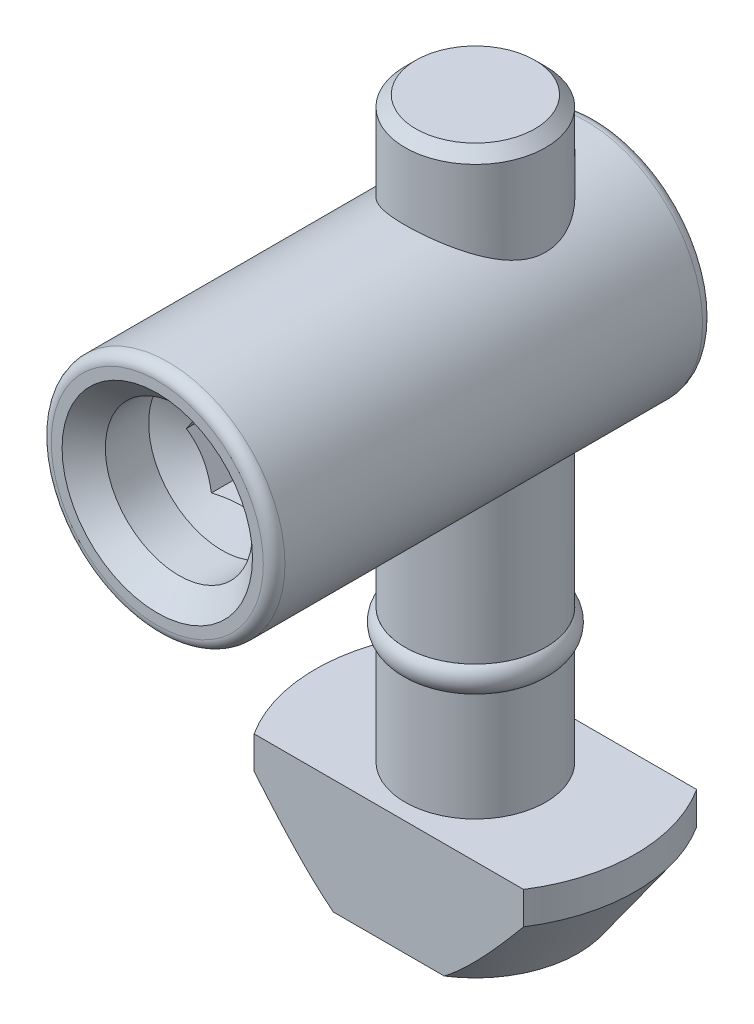
SolidWorks part; units mm, degrees
ref_plane "Спереди" through (0, 0, 0) normal (0, 0, 1) x (1, 0, 0)
ref_plane "Сверху" through (0, 0, 0) normal (0, 1, 0) x (1, 0, 0)
ref_plane "Справа" through (0, 0, 0) normal (1, 0, 0) x (0, 0, -1)
sketch "Эскиз3" plane through (0, 0, 0) normal (0, 0, 1) x (1, 0, 0)
  line L0 (0, 0) -> (-3.25, 0)
  line L1 (-3.25, 0) -> (-3.25, -20.5)
  line L2 (-3.25, -20.5) -> (-2.75, -20.5)
  line L3 (-2.75, -20.5) -> (-2.75, -21.7)
  line L4 (-2.75, -21.7) -> (-3.25, -21.7)
  line L5 (-3.25, -21.7) -> (-3.25, -26.7)
  line L7 (0, -32) -> (0, 0)
  line L8 (0, 0) -> (0, 5.384) construction
  line L9 (-3.25, -26.7) -> (-7.4, -26.7)
  line L10 (-7.4, -26.7) -> (-7.4, -28.2)
  line L11 (-7.4, -28.2) -> (-4.75, -32)
  line L12 (-4.75, -32) -> (0, -32)
  dimension "D1" = 6.5
  dimension "D2" = 1.2
  dimension "D3" = 32
  dimension "D4" = 0.5
  dimension "D5" = 5
  dimension "D6" = 5.3
  dimension "D7" = 1.5
  dimension "D8" = 1.5
  dimension "D9" = 14.8
revolve "Повернуть1" add sketch "Эскиз3" angle 360 about L8
sketch "Эскиз6" plane through (0, -32, 0) normal (0, -1, 0) x (1, 0, 0)
  line L1 (-7.4, -4) -> (7.4, -4)
  line L2 (-7.4, -4) -> (-7.4, 4)
  line L3 (-7.4, 4) -> (7.4, 4)
  line L4 (7.4, -4) -> (7.4, 4)
  line L5 (-7.4, -4) -> (7.4, 4) construction
  line L6 (-7.4, 4) -> (7.4, -4) construction
  circle A0 centre (0, 0) radius 7.4 construction
  point P0 (0, 0)
  point P6 (8.9355, 3.3962)
  dimension "D1" = 8
extrude "Вырез-Вытянуть1" cut sketch "Эскиз6" against normal up to surface (5.3 mm away) flip side to cut up to face at (0, -26.7, -7.4)
chamfer "Фаска1" distance 0.5 angle 45 1 edges at (0, 0, -3.25)
sketch "Эскиз12" plane through (0, 0, 0) normal (0, 0, 1) x (1, 0, 0)
  line L0 (2.75, 0) -> (-2.75, 0) construction
  circle A0 centre (0, -9) radius 5.4
  dimension "D1" = 10.8
  dimension "D2" = 9
extrude "Бобышка-Вытянуть2" add sketch "Эскиз12" along normal blind 14.7 and the other way blind 5.6
hole_wizard "Отверстие обработанное метчиком M81" positions "Эскиз13" profile "Эскиз14" tap size "M8" standard "ISO"
sketch "Эскиз13" plane through (0, 0, 14.7) normal (0, 0, 1) x (1, 0, 0)
  point P0 (0, -9)
cosmetic thread "Отверстие резьбы1" parameters "D1"=3, "D2"=8
sketch "Эскиз14" plane through (0, -9, 14.7) normal (1, 0, 0) x (0, -1, 0)
  line L0 (0, 0) -> (0, 5.0429)
  line L1 (0, 5.0429) -> (3.4, 3)
  line L2 (3.4, 3) -> (3.4, 1)
  line L3 (3.4, 1) -> (4.4, 0)
  line L5 (4.4, 0) -> (0, 0)
  line L6 (-3.4, 1) -> (-4.4, 0) construction
  line L10 (0, 5.0429) -> (-3.4, 3) construction
  line L11 (0, -6.35) -> (0, 107.95) construction
  dimension "Диаметр сверла" = 6.8
  dimension "Глубина сверла" = 3
  dimension "Диаметр передней зенковки" = 8.8
  dimension "Угол передней зенковки" = 90
  dimension "Угол заточки сверла" = 118
fillet "Скругление1" radius 0.5 2 edges at (5.4, -9, -5.6) (5.4, -9, 14.7)
sketch "Эскиз15" plane through (0, 0, 14.7) normal (0, 0, 1) x (1, 0, 0)
  line L1 (2.3094, -9) -> (1.1547, -7)
  line L2 (1.1547, -7) -> (-1.1547, -7)
  line L3 (-1.1547, -7) -> (-2.3094, -9)
  line L4 (-2.3094, -9) -> (-1.1547, -11)
  line L5 (-1.1547, -11) -> (1.1547, -11)
  line L6 (1.1547, -11) -> (2.3094, -9)
  circle A0 centre (0, -9) radius 2 construction
  dimension "D1" = 4
extrude "Вырез-Вытянуть2" cut sketch "Эскиз15" against normal blind 6
sketch "Эскиз16" plane through (0, 0, 0) normal (0, 0, 1) x (1, 0, 0)
  line L0 (-2.75, -20.5) -> (-3.25, -20.5)
  line L1 (-2.75, -20.5) -> (-2.75, -21.7) construction
  line L2 (-3.25, -21.7) -> (-2.75, -21.7)
  line L3 (-2.75, -21.7) -> (-2.75, -20.5)
  line L4 (-2.75, -20.5) -> (2.75, -20.5) construction
  line L7 (-3.25, -13.3125) -> (-3.25, -20.5) construction
  line L8 (3.25, -21.7) -> (-3.25, -21.7) construction
  line L9 (0, -20.5) -> (0, -21.7) construction
  arc A0 (-3.25, -20.5) -> (-3.25, -21.7) centre (-2.75, -21.1) ccw
  point P15 (-2.75, -21.1)
revolve "Повернуть2" add sketch "Эскиз16" angle 360 about L9
